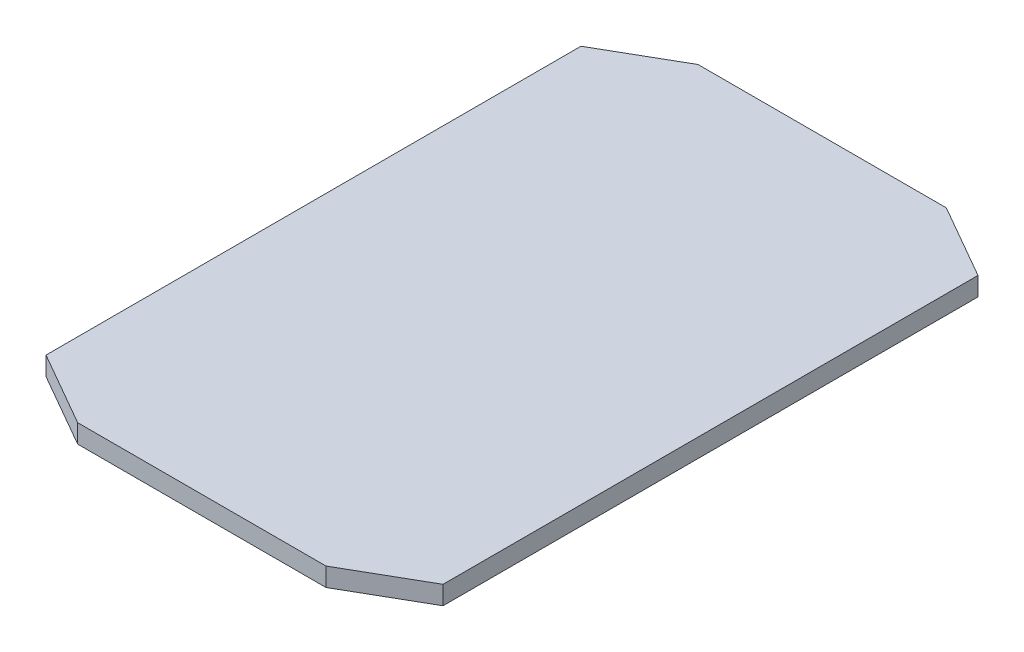
SolidWorks part; units mm, degrees
material "Custom Plastic"
ref_plane "Front Plane" through (0, 0, 0) normal (0, 0, 1) x (1, 0, 0)
ref_plane "Top Plane" through (0, 0, 0) normal (0, 1, 0) x (1, 0, 0)
ref_plane "Right Plane" through (0, 0, 0) normal (1, 0, 0) x (0, 0, -1)
sketch "Sketch1" plane through (0, 0, 0) normal (0, 1, 0) x (1, 0, 0)
  line L0 (-32, -43.1177) -> (-20.0119, -50)
  line L1 (-20.0119, -50) -> (20.0119, -50)
  line L2 (-32, -43.1177) -> (-32, 43.1177)
  line L3 (-20.0119, 50) -> (20.0119, 50)
  line L4 (32, -43.1177) -> (32, 43.1177)
  line L5 (-28.8545, -44.9235) -> (28.8545, 44.9235) construction
  line L6 (-28.4421, 45.1603) -> (28.4421, -45.1603) construction
  line L7 (-114.8204, 0) -> (150.9847, 0) construction
  line L8 (0, -72.5189) -> (0, 84.1411) construction
  line L9 (32, -43.1177) -> (20.0119, -50)
  line L10 (32, 43.1177) -> (20.0119, 50)
  line L11 (-32, 43.1177) -> (-20.0119, 50)
  point P0 (0, 0)
  dimension "D1" = 64
  dimension "D2" = 100
extrude "Boss-Extrude1" add sketch "Sketch1" along normal blind 3
ref_plane "Plane1" through (0, 0, 0) normal (0, 0, -1) x (-1, 0, 0)
ref_plane "Plane2" through (0, 0, 0) normal (0, 0, -1) x (-1, 0, 0)
